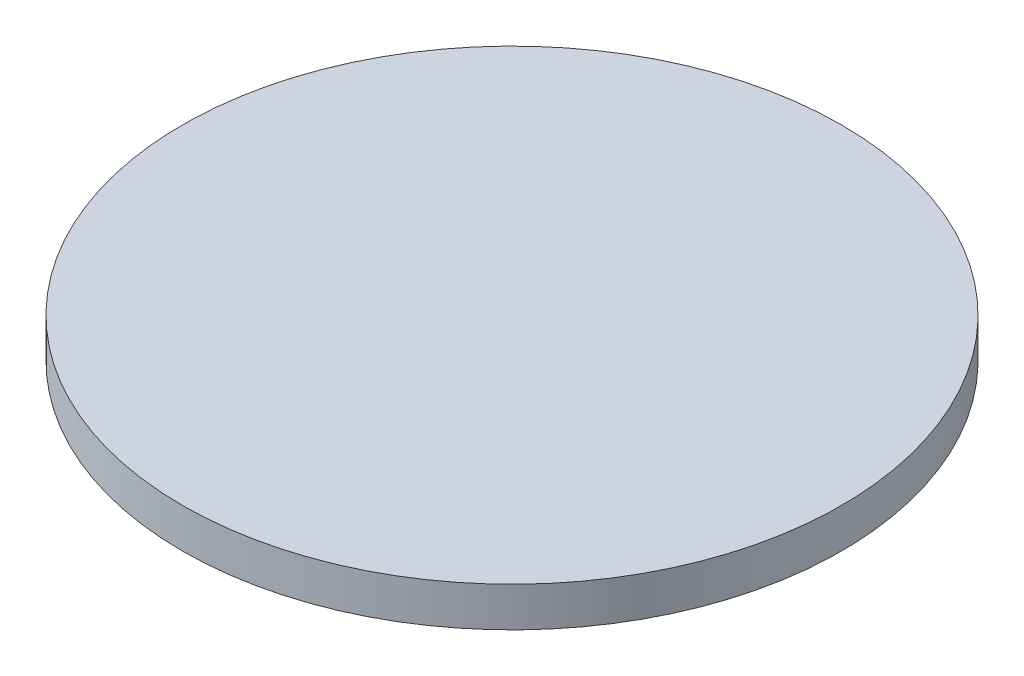
SolidWorks part; units mm, degrees
ref_plane "前视基准面" through (0, 0, 0) normal (0, 0, 1) x (1, 0, 0)
ref_plane "上视基准面" through (0, 0, 0) normal (0, 1, 0) x (1, 0, 0)
ref_plane "右视基准面" through (0, 0, 0) normal (1, 0, 0) x (0, 0, -1)
sketch "草图1" plane through (0, 0, 0) normal (0, 1, 0) x (1, 0, 0)
  circle A0 centre (0, 0) radius 25
  dimension "D1" = 50
extrude "凸台-拉伸1" add sketch "草图1" along normal blind 3
